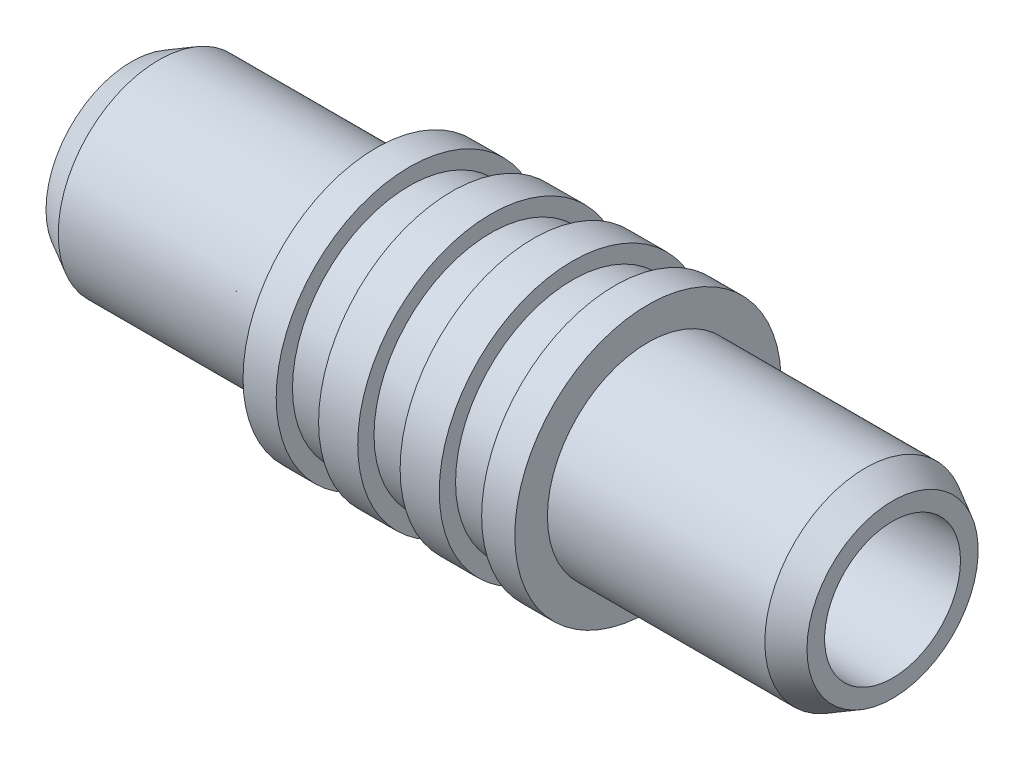
SolidWorks part; units mm, degrees
material "Polyetheretherketone (PEEK)"
ref_plane "Front Plane" through (0, 0, 0) normal (0, 0, 1) x (1, 0, 0)
ref_plane "Top Plane" through (0, 0, 0) normal (0, 1, 0) x (1, 0, 0)
ref_plane "Right Plane" through (0, 0, 0) normal (1, 0, 0) x (0, 0, -1)
sketch "Sketch1" plane through (0, 0, 0) normal (0, 0, 1) x (1, 0, 0)
  line L0 (0, 0) -> (88.0723, 0) construction
  line L1 (0, 2.0193) -> (17.78, 2.0193)
  line L2 (17.78, 2.0193) -> (17.78, 4.0005)
  line L3 (17.78, 4.0005) -> (16.51, 4.699)
  line L5 (6.35, 6.223) -> (0, 6.223)
  line L6 (0, 6.223) -> (0, 2.0193)
  line L7 (6.35, 6.223) -> (6.35, 4.699)
  line L8 (6.35, 4.699) -> (16.51, 4.699)
  dimension "D1" = 4.0386
  dimension "D2" = 1.27
  dimension "D3" = 6.35
  dimension "D4" = 8.001
  dimension "D5" = 12.446
  dimension "D6" = 11.43
  dimension "D7" = 9.398
revolve "Revolve1" add sketch "Sketch1" angle 360 about L0
mirror "Mirror1" about plane through (0, 6.223, 0) normal (1, 0, 0) of "Revolve1"
sketch "Sketch2" plane through (0, 0, 0) normal (0, 0, 1) x (1, 0, 0)
  line L0 (6.35, 6.223) -> (-6.35, 6.223) construction
  line L1 (-0.9906, 5.461) -> (0.9906, 5.461)
  line L2 (-0.9906, 5.461) -> (-0.9906, 6.985)
  line L3 (-0.9906, 6.985) -> (0.9906, 6.985)
  line L4 (0.9906, 5.461) -> (0.9906, 6.985)
  line L5 (-0.9906, 5.461) -> (0.9906, 6.985) construction
  line L6 (-0.9906, 6.985) -> (0.9906, 5.461) construction
  line L7 (0, 0) -> (19.6495, 0) construction
  line L9 (-4.8006, 5.461) -> (-2.8194, 5.461)
  line L10 (-4.8006, 5.461) -> (-4.8006, 6.985)
  line L11 (-4.8006, 6.985) -> (-2.8194, 6.985)
  line L12 (-2.8194, 5.461) -> (-2.8194, 6.985)
  line L13 (-4.8006, 5.461) -> (-2.8194, 6.985) construction
  line L14 (-4.8006, 6.985) -> (-2.8194, 5.461) construction
  line L15 (2.8194, 5.461) -> (4.8006, 5.461)
  line L16 (2.8194, 5.461) -> (2.8194, 6.985)
  line L17 (2.8194, 6.985) -> (4.8006, 6.985)
  line L18 (4.8006, 5.461) -> (4.8006, 6.985)
  line L19 (2.8194, 5.461) -> (4.8006, 6.985) construction
  line L20 (2.8194, 6.985) -> (4.8006, 5.461) construction
  point P0 (0, 6.223)
  point P10 (-3.81, 6.223)
  point P15 (3.81, 6.223)
  dimension "D1" = 10.922
  dimension "D2" = 1.9812
  dimension "D3" = 3.81
  dimension "D4" = 3.81
revolve "Cut-Revolve1" cut sketch "Sketch2" angle 360 about L7
sketch "Sketch3" plane through (17.78, 0, 0) normal (1, 0, 0) x (0, 0, -1)
  circle A0 centre (0, 0) radius 3.175
  dimension "D1" = 6.35
extrude "Cut-Extrude1" cut sketch "Sketch3" against normal blind 6.2992
